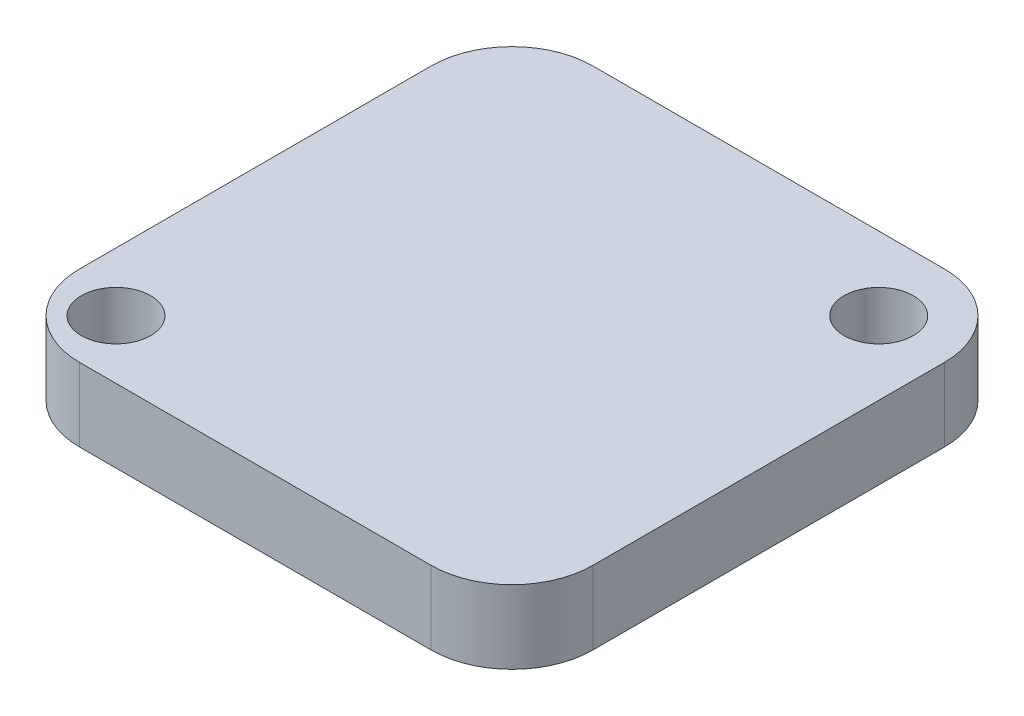
SolidWorks part; units mm, degrees
ref_plane "Front Plane" through (0, 0, 0) normal (0, 0, 1) x (1, 0, 0)
ref_plane "Top Plane" through (0, 0, 0) normal (0, 1, 0) x (1, 0, 0)
ref_plane "Right Plane" through (0, 0, 0) normal (1, 0, 0) x (0, 0, -1)
sketch "Sketch1" plane through (0, 0, 0) normal (0, 1, 0) x (1, 0, 0)
  line L0 (0, 0) -> (8.89, 0) construction
  line L1 (-6.09, 8.89) -> (6.09, 8.89)
  line L2 (-8.89, 6.09) -> (-8.89, -6.09)
  line L3 (-6.09, -8.89) -> (6.09, -8.89)
  line L4 (8.89, 6.09) -> (8.89, -6.09)
  line L5 (-8.89, 8.89) -> (8.89, -8.89) construction
  line L6 (-8.89, -8.89) -> (8.89, 8.89) construction
  line L7 (0, 0) -> (0, 8.89) construction
  circle A1 centre (6.35, 6.35) radius 1.2
  circle A4 centre (-6.858, -6.858) radius 1.2
  arc A6 (-8.89, -6.09) -> (-6.09, -8.89) centre (-6.09, -6.09) ccw
  arc A7 (6.09, -8.89) -> (8.89, -6.09) centre (6.09, -6.09) ccw
  arc A8 (6.09, 8.89) -> (8.89, 6.09) centre (6.09, 6.09) cw
  arc A9 (-6.09, 8.89) -> (-8.89, 6.09) centre (-6.09, 6.09) ccw
  point P0 (0, 0)
  point P29 (0, 0)
  point P30 (5.715, 6.9596)
  dimension "D4" = 2.4
  dimension "D5" = 2.8
  dimension "D1" = 17.78
  dimension "D2" = 17.78
  dimension "D3" = 2.54
  dimension "D6" = 2.54
extrude "Boss-Extrude1" add sketch "Sketch1" along normal blind 2.54
